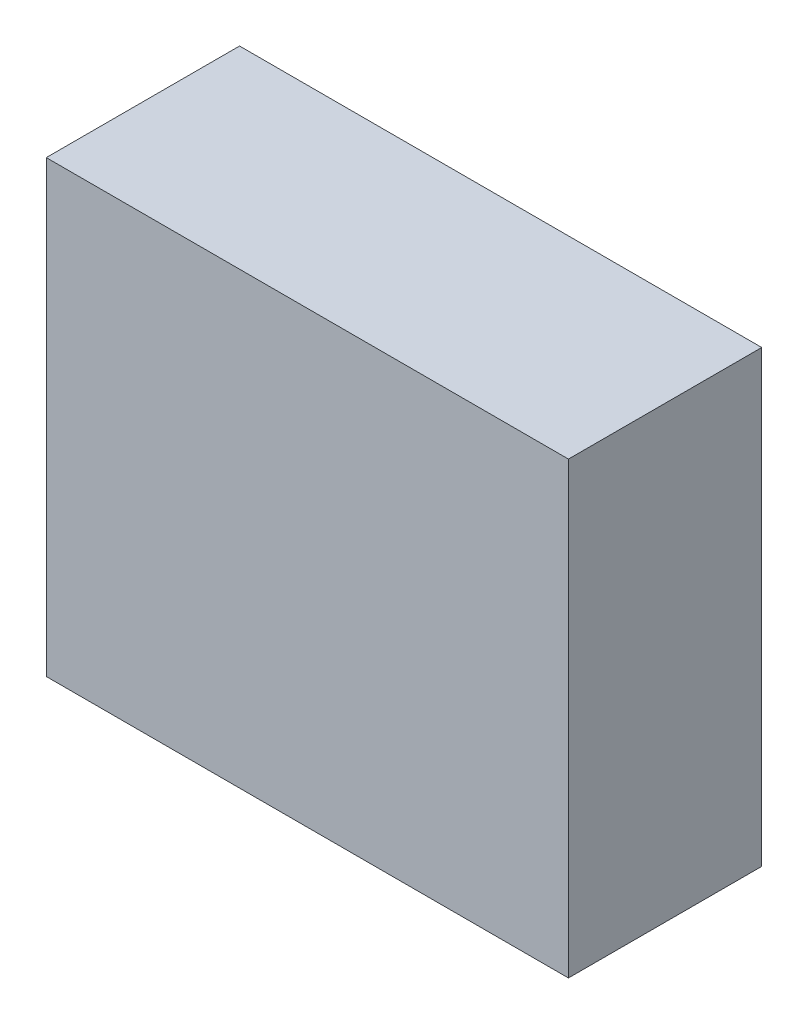
SolidWorks part; units mm, degrees
ref_plane "Front Plane" through (0, 0, 0) normal (0, 0, 1) x (1, 0, 0)
ref_plane "Top Plane" through (0, 0, 0) normal (0, 1, 0) x (1, 0, 0)
ref_plane "Right Plane" through (0, 0, 0) normal (1, 0, 0) x (0, 0, -1)
sketch "Sketch1" plane through (0, 0, 0) normal (0, 0, 1) x (1, 0, 0)
  line L1 (-32.4551, -19.7839) -> (21.577, -19.7839)
  line L2 (-32.4551, -19.7839) -> (-32.4551, 26.7172)
  line L3 (-32.4551, 26.7172) -> (21.577, 26.7172)
  line L4 (21.577, -19.7839) -> (21.577, 26.7172)
  point P4 (21.577, -19.7839)
extrude "Boss-Extrude1" add sketch "Sketch1" along normal blind 20
